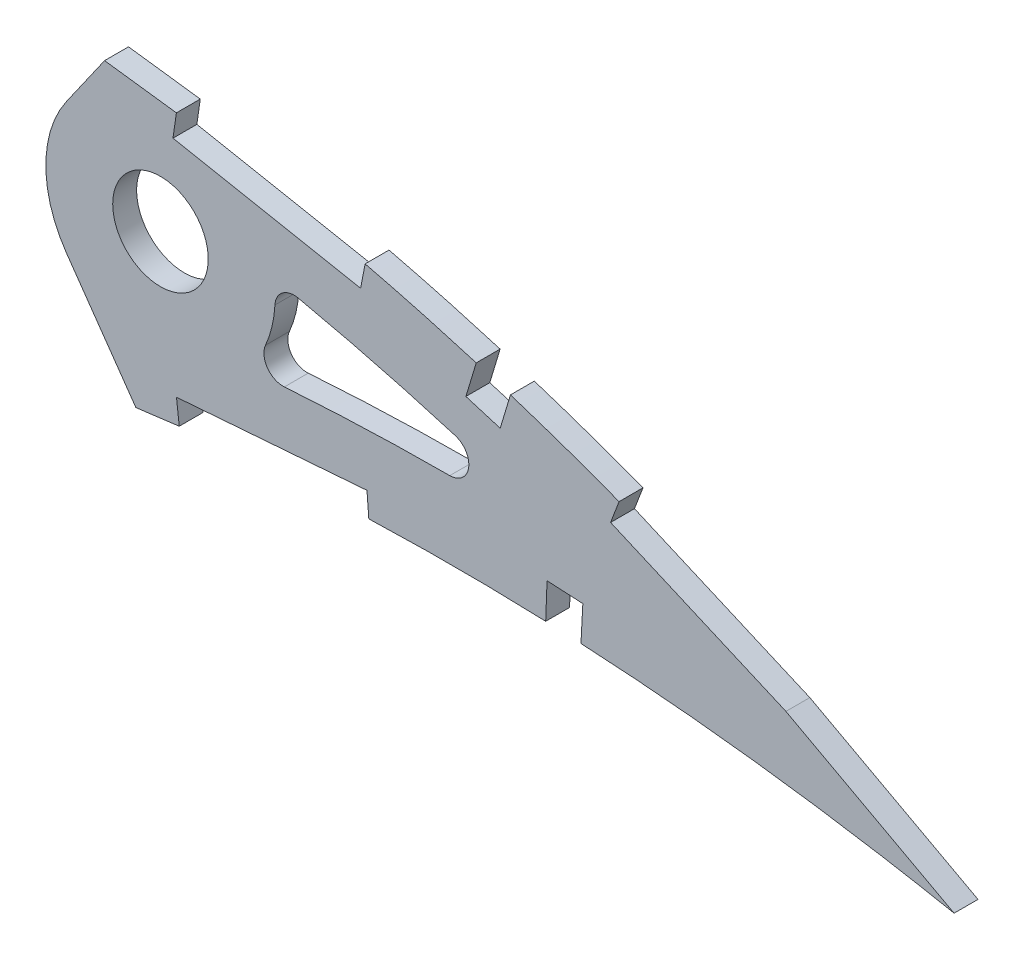
SolidWorks part; units mm, degrees
material "Plywood"
ref_plane "Front Plane" through (0, 0, 0) normal (0, 0, 1) x (1, 0, 0)
ref_plane "Top Plane" through (0, 0, 0) normal (0, 1, 0) x (1, 0, 0)
ref_plane "Right Plane" through (0, 0, 0) normal (1, 0, 0) x (0, 0, -1)
curve "Curve1"
  spline degree 3 poles (383.949, 0.5986, 0) (383.9196, 0.6168, 0) (383.802, 0.6894, 0) (383.5372, 0.8518, 0) (383.0962, 1.1224, 0) (382.4788, 1.4992, 0) (381.6856, 1.9812, 0) (380.716, 2.5651, 0) (379.5708, 3.249, 0) (378.2502, 4.0295, 0) (376.7543, 4.9032, 0) (375.0838, 5.8664, 0) (373.2387, 6.9137, 0) (371.2197, 8.0407, 0) (369.0276, 9.2423, 0) (366.6628, 10.5128, 0) (364.1261, 11.8459, 0) (361.4185, 13.2358, 0) (358.5405, 14.6749, 0) (355.4934, 16.1571, 0) (352.2782, 17.675, 0) (348.8962, 19.2207, 0) (345.3491, 20.7877, 0) (341.638, 22.3663, 0) (337.765, 23.9497, 0) (333.7318, 25.5289, 0) (329.5407, 27.0966, 0) (325.1933, 28.6428, 0) (320.6929, 30.1607, 0) (316.0417, 31.6403, 0) (311.2431, 33.0737, 0) (306.2997, 34.4516, 0) (301.2157, 35.767, 0) (295.9944, 37.0101, 0) (290.6401, 38.1728, 0) (285.1572, 39.2479, 0) (279.5502, 40.2249, 0) (273.8346, 41.1028, 0) (268.1025, 41.8331, 0) (262.3821, 42.5494, 0) (256.6703, 43.2222, 0) (250.8886, 43.8666, 0) (245.0428, 44.4788, 0) (239.1384, 45.057, 0) (233.1816, 45.5987, 0) (227.1785, 46.1022, 0) (221.135, 46.5647, 0) (215.0573, 46.9856, 0) (208.9515, 47.361, 0) (202.8242, 47.6908, 0) (196.6815, 47.9725, 0) (190.5298, 48.2044, 0) (184.3757, 48.385, 0) (178.2255, 48.5125, 0) (172.0859, 48.5861, 0) (165.9633, 48.6039, 0) (159.8643, 48.5655, 0) (153.7954, 48.4696, 0) (147.7632, 48.3149, 0) (141.7741, 48.1011, 0) (135.8345, 47.8283, 0) (129.951, 47.4942, 0) (124.1299, 47.1009, 0) (118.3778, 46.6469, 0) (112.701, 46.1319, 0) (107.1053, 45.5581, 0) (101.5971, 44.9239, 0) (96.1822, 44.2312, 0) (90.8666, 43.4813, 0) (85.6562, 42.6738, 0) (80.5566, 41.8111, 0) (75.5733, 40.894, 0) (70.7116, 39.9252, 0) (65.9768, 38.9049, 0) (61.3739, 37.8363, 0) (56.9076, 36.7211, 0) (52.5828, 35.5615, 0) (48.4038, 34.3602, 0) (44.375, 33.1199, 0) (40.5009, 31.842, 0) (36.7845, 30.5314, 0) (33.2304, 29.1889, 0) (29.8413, 27.8188, 0) (26.6212, 26.4228, 0) (23.5724, 25.0052, 0) (20.6984, 23.5677, 0) (18.0014, 22.1143, 0) (15.4839, 20.6472, 0) (13.1483, 19.1691, 0) (10.9958, 17.6837, 0) (9.0293, 16.1921, 0) (7.2493, 14.698, 0) (5.6571, 13.2036, 0) (4.255, 11.71, 0) (3.0428, 10.2198, 0) (2.0222, 8.7343, 0) (1.1933, 7.2547, 0) (0.558, 5.7822, 0) (0.1157, 4.3176, 0) (-0.1263, 2.863, 0) (-0.1866, 1.4174, 0) (-0.0621, 0.4718, 0) (0, 0, 0) knots 0 0 0 0 0.000254 0.001015 0.002283 0.004057 0.006331 0.009105 0.012374 0.016134 0.02038 0.025106 0.030306 0.035972 0.0421 0.048678 0.055702 0.06316 0.071046 0.07935 0.088063 0.097176 0.106678 0.116562 0.126814 0.137428 0.148394 0.1597 0.171338 0.183298 0.19557 0.208144 0.221012 0.234162 0.247587 0.261277 0.275223 0.289414 0.303771 0.317689 0.331784 0.34604 0.360444 0.374983 0.38964 0.404403 0.419257 0.434187 0.449177 0.464215 0.479284 0.49437 0.509458 0.524532 0.539579 0.554583 0.56953 0.584403 0.599191 0.613877 0.628447 0.642889 0.657186 0.671326 0.685294 0.699078 0.712665 0.726043 0.739198 0.752118 0.764792 0.777208 0.789356 0.801224 0.812804 0.824083 0.835055 0.84571 0.856038 0.866034 0.875689 0.884998 0.893953 0.902553 0.910789 0.918661 0.926166 0.933303 0.940071 0.946475 0.952518 0.958205 0.963547 0.968557 0.97325 0.977651 0.981787 0.985694 0.989415 0.993001 0.996508 1 1 1 1
curve "Curve2"
  spline degree 3 poles (0, 0, 0) (0.0986, -0.4654, 0) (0.2962, -1.3985, 0) (0.8332, -2.7416, 0) (1.5434, -4.0328, 0) (2.4415, -5.2686, 0) (3.5218, -6.4485, 0) (4.7818, -7.574, 0) (6.2202, -8.6443, 0) (7.8352, -9.659, 0) (9.6244, -10.6191, 0) (11.5859, -11.5241, 0) (13.7178, -12.3737, 0) (16.0178, -13.1667, 0) (18.4831, -13.9043, 0) (21.1113, -14.5848, 0) (23.8995, -15.2091, 0) (26.845, -15.7756, 0) (29.9446, -16.2848, 0) (33.195, -16.7366, 0) (36.593, -17.1311, 0) (40.1351, -17.4676, 0) (43.8179, -17.7467, 0) (47.6377, -17.9687, 0) (51.5909, -18.1343, 0) (55.6735, -18.2428, 0) (59.8817, -18.2959, 0) (64.2115, -18.2945, 0) (68.6589, -18.238, 0) (73.2199, -18.1297, 0) (77.8902, -17.9689, 0) (82.6657, -17.7575, 0) (87.5419, -17.4976, 0) (92.5144, -17.1902, 0) (97.5791, -16.8365, 0) (102.7313, -16.4394, 0) (107.9665, -16, 0) (113.2801, -15.5207, 0) (118.6674, -15.0039, 0) (124.1237, -14.4514, 0) (129.6442, -13.8657, 0) (135.2241, -13.2487, 0) (140.8584, -12.6036, 0) (146.5422, -11.9317, 0) (152.2705, -11.2369, 0) (158.0381, -10.5203, 0) (163.84, -9.7848, 0) (169.6711, -9.0339, 0) (175.5259, -8.2674, 0) (181.3995, -7.4908, 0) (187.2862, -6.7036, 0) (193.1809, -5.9096, 0) (199.0781, -5.1115, 0) (204.9721, -4.3094, 0) (210.8578, -3.5066, 0) (216.7295, -2.7054, 0) (222.5817, -1.9059, 0) (228.409, -1.112, 0) (234.2055, -0.3236, 0) (239.9659, 0.4577, 0) (245.6847, 1.2295, 0) (251.3565, 1.9909, 0) (256.9754, 2.7413, 0) (262.5357, 3.4812, 0) (267.9487, 4.188, 0) (273.2002, 4.8993, 0) (278.3079, 5.4825, 0) (283.3519, 5.9802, 0) (288.3377, 6.3883, 0) (293.259, 6.7125, 0) (298.1104, 6.9553, 0) (302.886, 7.1201, 0) (307.5799, 7.2116, 0) (312.186, 7.2323, 0) (316.6983, 7.1886, 0) (321.1107, 7.0842, 0) (325.4171, 6.9238, 0) (329.6115, 6.7126, 0) (333.688, 6.4566, 0) (337.6405, 6.1594, 0) (341.4634, 5.828, 0) (345.1508, 5.4673, 0) (348.6971, 5.0813, 0) (352.0971, 4.6782, 0) (355.3453, 4.2606, 0) (358.4369, 3.8354, 0) (361.3669, 3.4069, 0) (364.1307, 2.9806, 0) (366.7239, 2.5605, 0) (369.1422, 2.1521, 0) (371.3821, 1.7594, 0) (373.4394, 1.3862, 0) (375.3115, 1.0371, 0) (376.9946, 0.7139, 0) (378.4864, 0.4219, 0) (379.7842, 0.1625, 0) (380.886, -0.0608, 0) (381.79, -0.247, 0) (382.4947, -0.3932, 0) (382.9989, -0.4995, 0) (383.3019, -0.5627, 0) (383.4365, -0.5914, 0) (383.4701, -0.5986, 0) knots 0 0 0 0 0.003638 0.007293 0.011028 0.014901 0.018963 0.023258 0.027821 0.032679 0.037853 0.043362 0.049215 0.055422 0.061989 0.068918 0.076211 0.083868 0.091887 0.100266 0.109 0.118085 0.127515 0.137285 0.147388 0.157816 0.168563 0.179619 0.190977 0.202627 0.21456 0.226767 0.239236 0.251959 0.264924 0.27812 0.291536 0.30516 0.318981 0.332985 0.347163 0.361499 0.375981 0.390597 0.405333 0.420175 0.43511 0.450124 0.465203 0.480333 0.495501 0.51069 0.525887 0.541078 0.556247 0.571382 0.586466 0.601485 0.616424 0.631269 0.646007 0.660621 0.675098 0.689423 0.703582 0.716908 0.730009 0.742952 0.755726 0.76832 0.780724 0.792927 0.804916 0.816679 0.828204 0.839475 0.850481 0.861208 0.871639 0.881763 0.891564 0.901027 0.910139 0.918884 0.927249 0.935221 0.942785 0.949928 0.956638 0.962904 0.968712 0.974054 0.978918 0.983297 0.98718 0.990561 0.993433 0.995791 0.99763 0.998946 0.999737 1 1 1 1
sketch "Sketch1" plane through (0, 0, 0) normal (0, 0, 1) x (1, 0, 0)
  line L23 (383.4597, -0.5986) -> (387.1511, -1.386)
  line L24 (383.9386, 0.5986) -> (387.1511, -1.386)
  spline S4 degree 3 poles (0, 0) (0.0986, -0.4654) (0.2962, -1.3984) (0.8332, -2.7416) (1.5433, -4.0327) (2.4415, -5.2684) (3.5217, -6.4484) (4.7816, -7.5738) (6.22, -8.6441) (7.835, -9.6587) (9.6242, -10.6188) (11.5856, -11.5238) (13.7174, -12.3733) (16.0173, -13.1663) (18.4826, -13.9039) (21.1108, -14.5844) (23.8989, -15.2087) (26.8443, -15.7751) (29.9438, -16.2844) (33.1941, -16.7361) (36.592, -17.1306) (40.134, -17.4671) (43.8167, -17.7462) (47.6365, -17.9682) (51.5895, -18.1338) (55.672, -18.2423) (59.88, -18.2954) (64.2098, -18.294) (68.657, -18.2375) (73.2179, -18.1293) (77.8881, -17.9684) (82.6634, -17.757) (87.5395, -17.4972) (92.5119, -17.1897) (97.5764, -16.836) (102.7286, -16.439) (107.9636, -15.9995) (113.2771, -15.5202) (118.6642, -15.0035) (124.1204, -14.451) (129.6407, -13.8653) (135.2204, -13.2483) (140.8546, -12.6033) (146.5382, -11.9314) (152.2664, -11.2365) (158.0338, -10.52) (163.8356, -9.7845) (169.6665, -9.0336) (175.5212, -8.2672) (181.3946, -7.4906) (187.2811, -6.7034) (193.1757, -5.9095) (199.0727, -5.1113) (204.9666, -4.3092) (210.8521, -3.5065) (216.7237, -2.7054) (222.5757, -1.9059) (228.4028, -1.112) (234.1992, -0.3236) (239.9594, 0.4576) (245.6781, 1.2294) (251.3497, 1.9908) (256.9684, 2.7413) (262.5286, 3.4811) (267.9415, 4.1879) (273.1928, 4.8992) (278.3003, 5.4823) (283.3443, 5.98) (288.3299, 6.3881) (293.2511, 6.7123) (298.1023, 6.9552) (302.8778, 7.1199) (307.5715, 7.2114) (312.1776, 7.2321) (316.6897, 7.1884) (321.102, 7.084) (325.4083, 6.9236) (329.6026, 6.7124) (333.679, 6.4564) (337.6313, 6.1592) (341.4541, 5.8278) (345.1414, 5.4671) (348.6876, 5.0812) (352.0875, 4.6781) (355.3357, 4.2605) (358.4272, 3.8353) (361.3571, 3.4068) (364.1208, 2.9805) (366.7139, 2.5604) (369.1322, 2.1521) (371.372, 1.7594) (373.4293, 1.3862) (375.3013, 1.0371) (376.9844, 0.7139) (378.4761, 0.4219) (379.7739, 0.1625) (380.8757, -0.0608) (381.7796, -0.247) (382.4844, -0.3932) (382.9885, -0.4994) (383.2915, -0.5627) (383.4261, -0.5914) (383.4597, -0.5986) knots 0 0 0 0 0.003638 0.007293 0.011028 0.014901 0.018963 0.023258 0.027821 0.032679 0.037853 0.043362 0.049215 0.055422 0.061989 0.068918 0.076211 0.083868 0.091887 0.100266 0.109 0.118085 0.127515 0.137285 0.147388 0.157816 0.168563 0.179619 0.190977 0.202627 0.21456 0.226767 0.239236 0.251959 0.264924 0.27812 0.291536 0.30516 0.318981 0.332985 0.347163 0.361499 0.375981 0.390597 0.405333 0.420175 0.43511 0.450124 0.465203 0.480333 0.495501 0.51069 0.525887 0.541078 0.556247 0.571382 0.586466 0.601485 0.616424 0.631269 0.646007 0.660621 0.675098 0.689423 0.703582 0.716908 0.730009 0.742952 0.755726 0.76832 0.780724 0.792927 0.804916 0.816679 0.828204 0.839475 0.850481 0.861208 0.871639 0.881763 0.891564 0.901027 0.910139 0.918884 0.927249 0.935221 0.942785 0.949928 0.956638 0.962904 0.968712 0.974054 0.978918 0.983297 0.98718 0.990561 0.993433 0.995791 0.99763 0.998946 0.999737 1 1 1 1
  spline S5 degree 3 poles (383.9386, 0.5986) (383.9092, 0.6167) (383.7916, 0.6893) (383.5268, 0.8518) (383.0858, 1.1223) (382.4685, 1.4991) (381.6752, 1.9811) (380.7057, 2.565) (379.5606, 3.2489) (378.24, 4.0294) (376.7441, 4.9031) (375.0736, 5.8662) (373.2286, 6.9135) (371.2097, 8.0405) (369.0176, 9.242) (366.6529, 10.5125) (364.1162, 11.8456) (361.4087, 13.2354) (358.5307, 14.6745) (355.4837, 16.1566) (352.2687, 17.6745) (348.8867, 19.2201) (345.3398, 20.7871) (341.6288, 22.3657) (337.7559, 23.949) (333.7228, 25.5282) (329.5317, 27.0959) (325.1845, 28.642) (320.6843, 30.1598) (316.0332, 31.6395) (311.2346, 33.0728) (306.2914, 34.4507) (301.2076, 35.766) (295.9864, 37.0091) (290.6322, 38.1717) (285.1495, 39.2469) (279.5426, 40.2238) (273.8272, 41.1017) (268.0952, 41.832) (262.375, 42.5482) (256.6633, 43.2211) (250.8818, 43.8654) (245.0361, 44.4776) (239.1319, 45.0558) (233.1753, 45.5974) (227.1724, 46.1009) (221.129, 46.5635) (215.0515, 46.9843) (208.9459, 47.3597) (202.8187, 47.6895) (196.6762, 47.9712) (190.5246, 48.2031) (184.3707, 48.3836) (178.2206, 48.5111) (172.0812, 48.5848) (165.9588, 48.6026) (159.86, 48.5642) (153.7912, 48.4683) (147.7592, 48.3136) (141.7702, 48.0998) (135.8308, 47.827) (129.9475, 47.4929) (124.1266, 47.0997) (118.3746, 46.6456) (112.6979, 46.1306) (107.1024, 45.5568) (101.5944, 44.9227) (96.1796, 44.23) (90.8641, 43.4801) (85.6539, 42.6727) (80.5544, 41.81) (75.5713, 40.8929) (70.7097, 39.9241) (65.975, 38.9039) (61.3722, 37.8353) (56.906, 36.7201) (52.5814, 35.5606) (48.4025, 34.3593) (44.3738, 33.119) (40.4998, 31.8412) (36.7835, 30.5306) (33.2295, 29.1881) (29.8405, 27.818) (26.6204, 26.4221) (23.5718, 25.0045) (20.6979, 23.5671) (18.0009, 22.1137) (15.4834, 20.6466) (13.148, 19.1685) (10.9955, 17.6833) (9.029, 16.1917) (7.2491, 14.6976) (5.657, 13.2033) (4.2548, 11.7097) (3.0427, 10.2196) (2.0221, 8.734) (1.1932, 7.2545) (0.558, 5.782) (0.1157, 4.3174) (-0.1263, 2.8629) (-0.1866, 1.4173) (-0.0621, 0.4717) (0, 0) knots 0 0 0 0 0.000254 0.001015 0.002283 0.004057 0.006331 0.009105 0.012374 0.016134 0.02038 0.025106 0.030306 0.035972 0.0421 0.048678 0.055702 0.06316 0.071046 0.07935 0.088063 0.097176 0.106678 0.116562 0.126814 0.137428 0.148394 0.1597 0.171338 0.183298 0.19557 0.208144 0.221012 0.234162 0.247587 0.261277 0.275223 0.289414 0.303771 0.317689 0.331784 0.34604 0.360444 0.374983 0.38964 0.404403 0.419257 0.434187 0.449177 0.464215 0.479284 0.49437 0.509458 0.524532 0.539579 0.554583 0.56953 0.584403 0.599191 0.613877 0.628447 0.642889 0.657186 0.671326 0.685294 0.699078 0.712665 0.726043 0.739198 0.752118 0.764792 0.777208 0.789356 0.801224 0.812804 0.824083 0.835055 0.84571 0.856038 0.866034 0.875689 0.884998 0.893953 0.902553 0.910789 0.918661 0.926166 0.933303 0.940071 0.946475 0.952518 0.958205 0.963547 0.968557 0.97325 0.977651 0.981787 0.985694 0.989415 0.993001 0.996508 1 1 1 1
extrude "Boss-Extrude1" add sketch "Sketch1" along normal blind 3.175
sketch "Sketch3" plane through (0, 0, 0) normal (0, 0, -1) x (-1, 0, 0)
  circle A1 centre (-272.4199, 26.2554) radius 6.35
extrude "Cut-Extrude2" cut sketch "Sketch3" against normal blind 7.62
sketch "Sketch4" plane through (0, 0, 3.175) normal (0, 0, 1) x (1, 0, 0)
  line L0 (272.4199, 26.2554) -> (275.6183, 26.2554)
  line L1 (259.936, 34.9967) -> (264.9932, 42.2191)
  line L2 (259.936, 17.5141) -> (269.1511, 4.3535)
  circle A0 centre (272.4199, 26.2554) radius 6.35 construction
  circle A1 centre (272.4199, 26.2554) radius 6.35
  circle A2 centre (272.4199, 26.2554) radius 15.24
  spline S0 degree 3 poles (-2900.5811, -762.1564) (60.7171, 58.1372) (-7.1311, 17.1797) (0.8332, -2.7416) (1.5433, -4.0327) (2.4415, -5.2684) (3.5217, -6.4484) (4.7816, -7.5738) (6.22, -8.6441) (7.835, -9.6587) (9.6242, -10.6188) (11.5856, -11.5238) (13.7174, -12.3733) (16.0173, -13.1663) (18.4826, -13.9039) (21.1108, -14.5844) (23.8989, -15.2087) (26.8443, -15.7751) (29.9438, -16.2844) (33.1941, -16.7361) (36.592, -17.1306) (40.134, -17.4671) (43.8167, -17.7462) (47.6365, -17.9682) (51.5895, -18.1338) (55.672, -18.2423) (59.88, -18.2954) (64.2098, -18.294) (68.657, -18.2375) (73.2179, -18.1293) (77.8881, -17.9684) (82.6634, -17.757) (87.5395, -17.4972) (92.5119, -17.1897) (97.5764, -16.836) (102.7286, -16.439) (107.9636, -15.9995) (113.2771, -15.5202) (118.6642, -15.0035) (124.1204, -14.451) (129.6407, -13.8653) (135.2204, -13.2483) (140.8546, -12.6033) (146.5382, -11.9314) (152.2664, -11.2365) (158.0338, -10.52) (163.8356, -9.7845) (169.6665, -9.0336) (175.5212, -8.2672) (181.3946, -7.4906) (187.2811, -6.7034) (193.1757, -5.9095) (199.0727, -5.1113) (204.9666, -4.3092) (210.8521, -3.5065) (216.7237, -2.7054) (222.5757, -1.9059) (228.4028, -1.112) (234.1992, -0.3236) (239.9594, 0.4576) (245.6781, 1.2294) (251.3497, 1.9908) (256.9684, 2.7413) (262.5286, 3.4811) (267.9415, 4.1879) (273.1928, 4.8992) (278.3003, 5.4823) (283.3443, 5.98) (288.3299, 6.3881) (293.2511, 6.7123) (298.1023, 6.9552) (302.8778, 7.1199) (307.5715, 7.2114) (312.1776, 7.2321) (316.6897, 7.1884) (321.102, 7.084) (325.4083, 6.9236) (329.6026, 6.7124) (333.679, 6.4564) (337.6313, 6.1592) (341.4541, 5.8278) (345.1414, 5.4671) (348.6876, 5.0812) (352.0875, 4.6781) (355.3357, 4.2605) (358.4272, 3.8353) (361.3571, 3.4068) (364.1208, 2.9805) (366.7139, 2.5604) (369.1322, 2.1521) (371.372, 1.7594) (373.4293, 1.3862) (375.3013, 1.0371) (376.9844, 0.7139) (378.4761, 0.4219) (379.7739, 0.1625) (380.8757, -0.0608) (381.7796, -0.247) (382.4844, -0.3932) (382.9885, -0.4994) (397.7614, -3.5828) (410.8952, -13.5854) (1047.3532, 2924.2375) knots -0.152541 -0.152541 -0.152541 -0.152541 0.003638 0.007293 0.011028 0.014901 0.018963 0.023258 0.027821 0.032679 0.037853 0.043362 0.049215 0.055422 0.061989 0.068918 0.076211 0.083868 0.091887 0.100266 0.109 0.118085 0.127515 0.137285 0.147388 0.157816 0.168563 0.179619 0.190977 0.202627 0.21456 0.226767 0.239236 0.251959 0.264924 0.27812 0.291536 0.30516 0.318981 0.332985 0.347163 0.361499 0.375981 0.390597 0.405333 0.420175 0.43511 0.450124 0.465203 0.480333 0.495501 0.51069 0.525887 0.541078 0.556247 0.571382 0.586466 0.601485 0.616424 0.631269 0.646007 0.660621 0.675098 0.689423 0.703582 0.716908 0.730009 0.742952 0.755726 0.76832 0.780724 0.792927 0.804916 0.816679 0.828204 0.839475 0.850481 0.861208 0.871639 0.881763 0.891564 0.901027 0.910139 0.918884 0.927249 0.935221 0.942785 0.949928 0.956638 0.962904 0.968712 0.974054 0.978918 0.983297 0.98718 0.990561 0.993433 0.995791 0.99763 0.998946 0.999737 1.113214 1.113214 1.113214 1.113214 only from (0, 0) to (383.4597, -0.5986) construction
  spline S1 degree 3 poles (1998.8466, 2527.3991) (408.7537, -22.1004) (397.8856, -7.9557) (383.5268, 0.8518) (383.0858, 1.1223) (382.4685, 1.4991) (381.6752, 1.9811) (380.7057, 2.565) (379.5606, 3.2489) (378.24, 4.0294) (376.7441, 4.9031) (375.0736, 5.8662) (373.2286, 6.9135) (371.2097, 8.0405) (369.0176, 9.242) (366.6529, 10.5125) (364.1162, 11.8456) (361.4087, 13.2354) (358.5307, 14.6745) (355.4837, 16.1566) (352.2687, 17.6745) (348.8867, 19.2201) (345.3398, 20.7871) (341.6288, 22.3657) (337.7559, 23.949) (333.7228, 25.5282) (329.5317, 27.0959) (325.1845, 28.642) (320.6843, 30.1598) (316.0332, 31.6395) (311.2346, 33.0728) (306.2914, 34.4507) (301.2076, 35.766) (295.9864, 37.0091) (290.6322, 38.1717) (285.1495, 39.2469) (279.5426, 40.2238) (273.8272, 41.1017) (268.0952, 41.832) (262.375, 42.5482) (256.6633, 43.2211) (250.8818, 43.8654) (245.0361, 44.4776) (239.1319, 45.0558) (233.1753, 45.5974) (227.1724, 46.1009) (221.129, 46.5635) (215.0515, 46.9843) (208.9459, 47.3597) (202.8187, 47.6895) (196.6762, 47.9712) (190.5246, 48.2031) (184.3707, 48.3836) (178.2206, 48.5111) (172.0812, 48.5848) (165.9588, 48.6026) (159.86, 48.5642) (153.7912, 48.4683) (147.7592, 48.3136) (141.7702, 48.0998) (135.8308, 47.827) (129.9475, 47.4929) (124.1266, 47.0997) (118.3746, 46.6456) (112.6979, 46.1306) (107.1024, 45.5568) (101.5944, 44.9227) (96.1796, 44.23) (90.8641, 43.4801) (85.6539, 42.6727) (80.5544, 41.81) (75.5713, 40.8929) (70.7097, 39.9241) (65.975, 38.9039) (61.3722, 37.8353) (56.906, 36.7201) (52.5814, 35.5606) (48.4025, 34.3593) (44.3738, 33.119) (40.4998, 31.8412) (36.7835, 30.5306) (33.2295, 29.1881) (29.8405, 27.818) (26.6204, 26.4221) (23.5718, 25.0045) (20.6979, 23.5671) (18.0009, 22.1137) (15.4834, 20.6466) (13.148, 19.1685) (10.9955, 17.6833) (9.029, 16.1917) (7.2491, 14.6976) (5.657, 13.2033) (4.2548, 11.7097) (3.0427, 10.2196) (2.0221, 8.734) (1.1932, 7.2545) (0.558, 5.782) (0.1157, 4.3174) (-0.1263, 2.8629) (-1.0184, -18.5368) (76.7539, -34.5403) (-2989.0976, -246.1964) knots -0.121519 -0.121519 -0.121519 -0.121519 0.000254 0.001015 0.002283 0.004057 0.006331 0.009105 0.012374 0.016134 0.02038 0.025106 0.030306 0.035972 0.0421 0.048678 0.055702 0.06316 0.071046 0.07935 0.088063 0.097176 0.106678 0.116562 0.126814 0.137428 0.148394 0.1597 0.171338 0.183298 0.19557 0.208144 0.221012 0.234162 0.247587 0.261277 0.275223 0.289414 0.303771 0.317689 0.331784 0.34604 0.360444 0.374983 0.38964 0.404403 0.419257 0.434187 0.449177 0.464215 0.479284 0.49437 0.509458 0.524532 0.539579 0.554583 0.56953 0.584403 0.599191 0.613877 0.628447 0.642889 0.657186 0.671326 0.685294 0.699078 0.712665 0.726043 0.739198 0.752118 0.764792 0.777208 0.789356 0.801224 0.812804 0.824083 0.835055 0.84571 0.856038 0.866034 0.875689 0.884998 0.893953 0.902553 0.910789 0.918661 0.926166 0.933303 0.940071 0.946475 0.952518 0.958205 0.963547 0.968557 0.97325 0.977651 0.981787 0.985694 0.989415 0.993001 0.996508 1.146107 1.146107 1.146107 1.146107 only from (383.9386, 0.5986) to (0, 0) construction
  spline S2 degree 3 poles (161.4571, -10.0855) (162.2464, -9.9853) (164.9804, -9.6371) (169.6665, -9.0336) (175.5212, -8.2672) (181.3946, -7.4906) (187.2811, -6.7034) (193.1757, -5.9095) (199.0727, -5.1113) (204.9666, -4.3092) (210.8521, -3.5065) (216.7237, -2.7054) (222.5757, -1.9059) (228.4028, -1.112) (234.1992, -0.3236) (239.9594, 0.4576) (245.6781, 1.2294) (251.3497, 1.9908) (256.9684, 2.7413) (262.5286, 3.4811) (267.9415, 4.1879) (273.1928, 4.8992) (278.3003, 5.4823) (283.3443, 5.98) (288.3299, 6.3881) (293.2511, 6.7123) (298.1023, 6.9552) (302.8778, 7.1199) (307.5715, 7.2114) (312.1776, 7.2321) (316.6897, 7.1884) (321.102, 7.084) (325.4083, 6.9236) (329.6026, 6.7124) (333.679, 6.4564) (337.6313, 6.1592) (341.4541, 5.8278) (345.1414, 5.4671) (348.6876, 5.0812) (352.0875, 4.6781) (355.3357, 4.2605) (358.4272, 3.8353) (361.3571, 3.4068) (364.1208, 2.9805) (366.7139, 2.5604) (369.1322, 2.1521) (371.372, 1.7594) (373.4293, 1.3862) (375.3013, 1.0371) (376.9844, 0.7139) (378.4761, 0.4219) (379.7739, 0.1625) (380.8757, -0.0608) (381.7796, -0.247) (382.4844, -0.3932) (382.9885, -0.4994) (383.2915, -0.5627) (383.4261, -0.5914) (383.4597, -0.5986) knots 0.429016 0.429016 0.429016 0.429016 0.43511 0.450124 0.465203 0.480333 0.495501 0.51069 0.525887 0.541078 0.556247 0.571382 0.586466 0.601485 0.616424 0.631269 0.646007 0.660621 0.675098 0.689423 0.703582 0.716908 0.730009 0.742952 0.755726 0.76832 0.780724 0.792927 0.804916 0.816679 0.828204 0.839475 0.850481 0.861208 0.871639 0.881763 0.891564 0.901027 0.910139 0.918884 0.927249 0.935221 0.942785 0.949928 0.956638 0.962904 0.968712 0.974054 0.978918 0.983297 0.98718 0.990561 0.993433 0.995791 0.99763 0.998946 0.999737 1 1 1 1
  spline S3 degree 3 poles (383.9386, 0.5986) (383.9092, 0.6167) (383.7916, 0.6893) (383.5268, 0.8518) (383.0858, 1.1223) (382.4685, 1.4991) (381.6752, 1.9811) (380.7057, 2.565) (379.5606, 3.2489) (378.24, 4.0294) (376.7441, 4.9031) (375.0736, 5.8662) (373.2286, 6.9135) (371.2097, 8.0405) (369.0176, 9.242) (366.6529, 10.5125) (364.1162, 11.8456) (361.4087, 13.2354) (358.5307, 14.6745) (355.4837, 16.1566) (352.2687, 17.6745) (348.8867, 19.2201) (345.3398, 20.7871) (341.6288, 22.3657) (337.7559, 23.949) (333.7228, 25.5282) (329.5317, 27.0959) (325.1845, 28.642) (320.6843, 30.1598) (316.0332, 31.6395) (311.2346, 33.0728) (306.2914, 34.4507) (301.2076, 35.766) (295.9864, 37.0091) (290.6322, 38.1717) (285.1495, 39.2469) (279.5426, 40.2238) (273.8272, 41.1017) (268.0952, 41.832) (262.375, 42.5482) (256.6633, 43.2211) (250.8818, 43.8654) (245.0361, 44.4776) (239.1319, 45.0558) (233.1753, 45.5974) (227.1724, 46.1009) (221.129, 46.5635) (215.0515, 46.9843) (208.9459, 47.3597) (202.8187, 47.6895) (196.6762, 47.9712) (190.5246, 48.2031) (184.3707, 48.3836) (178.2206, 48.5111) (172.0812, 48.5848) (165.9588, 48.6026) (159.86, 48.5642) (153.5038, 48.4638) (149.182, 48.3499) (146.8838, 48.276) knots 0 0 0 0 0.000254 0.001015 0.002283 0.004057 0.006331 0.009105 0.012374 0.016134 0.02038 0.025106 0.030306 0.035972 0.0421 0.048678 0.055702 0.06316 0.071046 0.07935 0.088063 0.097176 0.106678 0.116562 0.126814 0.137428 0.148394 0.1597 0.171338 0.183298 0.19557 0.208144 0.221012 0.234162 0.247587 0.261277 0.275223 0.289414 0.303771 0.317689 0.331784 0.34604 0.360444 0.374983 0.38964 0.404403 0.419257 0.434187 0.449177 0.464215 0.479284 0.49437 0.509458 0.524532 0.539579 0.554583 0.56953 0.584403 0.601304 0.601304 0.601304 0.601304
  spline S4 degree 1 poles (378.5989, -8.0451) (147.21, 38.1213) knots 0 0 1 1 construction
  spline S5 degree 3 poles (378.5989, -8.0451) (378.472, -7.9667) (378.2234, -7.8142) (377.6805, -7.4812) (376.7611, -6.9205) (374.9109, -5.8032) (371.1788, -3.5966) (363.6516, 0.6712) (348.2892, 8.639) (330.0962, 16.359) (311.3792, 22.5636) (297.107, 26.4342) (285.0856, 28.9814) (276.5539, 30.4164) (271.7323, 31.12) (268.0333, 31.5987) (264.2273, 32.0776) (259.2208, 32.6948) (250.4292, 33.7129) (237.8617, 35.009) (222.7587, 36.2937) (202.6061, 37.6338) (177.3909, 38.5745) (157.2697, 38.4445) (147.21, 38.1213) knots 0 0 0 0 0.001174 0.002349 0.004698 0.009395 0.018791 0.037581 0.075163 0.150326 0.187907 0.225489 0.26307 0.281861 0.291256 0.300652 0.310047 0.319443 0.338233 0.375815 0.413396 0.450978 0.526141 0.601304 0.601304 0.601304 0.601304
  spline S6 degree 1 poles (160.178, -0.0063) (385.5793, 9.3379) knots 0 0 1 1 construction
  spline S7 degree 3 poles (160.178, -0.0063) (169.3975, 1.1637) (187.8091, 3.6001) (210.885, 6.7523) (229.3545, 9.2731) (243.2292, 11.1537) (254.7583, 12.7013) (262.905, 13.7751) (267.4672, 14.3775) (270.981, 14.8497) (274.6098, 15.2908) (279.3773, 15.8089) (285.3756, 16.3645) (292.5728, 16.8641) (302.1885, 17.3159) (314.2133, 17.4755) (333.4344, 16.8874) (352.5648, 15.0706) (369.1185, 12.5101) (377.3698, 10.9967) (381.4564, 10.1902) (383.3728, 9.7984) (384.2388, 9.6192) (384.6955, 9.524) (385.0455, 9.4502) (385.329, 9.391) (385.4982, 9.3552) (385.5793, 9.3379) knots 0.429016 0.429016 0.429016 0.429016 0.500389 0.571762 0.607448 0.643135 0.678821 0.696665 0.705586 0.714508 0.723429 0.732351 0.750194 0.768038 0.785881 0.821567 0.857254 0.928627 0.964313 0.982157 0.991078 0.995539 0.996654 0.99777 0.998885 0.999442 1 1 1 1
  dimension "D1" = 30.48
  dimension "D2" = 55
  dimension "D3" = 55
  dimension "D4" = 10.16
extrude "Cut-Extrude3" cut sketch "Sketch4" against normal through all
sketch "Sketch5" plane through (0, 0, 3.175) normal (0, 0, 1) x (1, 0, 0)
  line L0 (274.5345, 40.976) -> (274.083, 37.8333)
  line L1 (274.083, 37.8333) -> (299.0226, 33.019)
  line L2 (299.0226, 33.019) -> (299.6244, 36.1364)
  line L3 (274.9174, 5.0903) -> (274.5453, 8.2434)
  line L4 (274.5453, 8.2434) -> (299.8708, 10.1869)
  line L5 (299.8708, 10.1869) -> (300.1138, 7.0212)
  line L6 (333.3826, 25.6462) -> (332.2514, 22.6795)
  line L7 (332.2514, 22.6795) -> (355.5602, 12.5869)
  line L8 (355.5602, 12.5869) -> (377.9168, 0.5311)
  line L9 (377.9168, 0.5311) -> (379.5381, 3.2609)
  line L10 (355.5602, 12.5869) -> (356.9478, 15.4426)
  line L11 (314.393, 32.1244) -> (313.0177, 27.5648)
  line L12 (313.0177, 27.5648) -> (317.5773, 26.1895)
  line L13 (317.5773, 26.1895) -> (318.9408, 30.7101)
  line L14 (323.625, 6.9875) -> (323.8072, 11.7465)
  line L15 (323.8072, 11.7465) -> (328.5631, 11.4961)
  line L16 (328.5631, 11.4961) -> (328.3145, 6.7742)
  line L17 (333.3826, 25.6462) -> (318.9408, 30.7101) construction
  line L18 (314.393, 32.1244) -> (299.6244, 36.1364) construction
  line L19 (355.5602, 12.5869) -> (351.7355, 4.7158)
  line L20 (351.7355, 4.7158) -> (328.3145, 6.7742) construction
  line L21 (323.625, 6.9875) -> (300.1138, 7.0212) construction
  circle A0 centre (272.4199, 26.2554) radius 6.35 construction
  circle A1 centre (272.4199, 26.2554) radius 6.35
  spline S0 degree 3 poles (-210.4395, 1941.1642) (121.3297, -52.1941) (196.4933, -3.8575) (278.3003, 5.4823) (283.3443, 5.98) (288.3299, 6.3881) (293.2511, 6.7123) (298.1023, 6.9552) (302.8778, 7.1199) (307.5715, 7.2114) (312.1776, 7.2321) (316.6897, 7.1884) (321.102, 7.084) (325.4083, 6.9236) (329.6026, 6.7124) (333.679, 6.4564) (337.6313, 6.1592) (341.4541, 5.8278) (345.1414, 5.4671) (348.6876, 5.0812) (352.0875, 4.6781) (355.3357, 4.2605) (358.4272, 3.8353) (361.3571, 3.4068) (364.1208, 2.9805) (366.7139, 2.5604) (369.1322, 2.1521) (371.372, 1.7594) (373.4293, 1.3862) (375.3013, 1.0371) (376.9844, 0.7139) (378.4761, 0.4219) (379.7739, 0.1625) (380.8757, -0.0608) (381.7796, -0.247) (382.4844, -0.3932) (382.9885, -0.4994) (395.9321, -3.201) (407.582, -11.1888) (835.0263, 1947.3652) knots 0.11236 0.11236 0.11236 0.11236 0.716908 0.730009 0.742952 0.755726 0.76832 0.780724 0.792927 0.804916 0.816679 0.828204 0.839475 0.850481 0.861208 0.871639 0.881763 0.891564 0.901027 0.910139 0.918884 0.927249 0.935221 0.942785 0.949928 0.956638 0.962904 0.968712 0.974054 0.978918 0.983297 0.98718 0.990561 0.993433 0.995791 0.99763 0.998946 0.999737 1.098901 1.098901 1.098901 1.098901 only from (269.1511, 4.3535) to (383.4597, -0.5986) construction
  spline S1 degree 3 poles (1469.2762, 1679.7392) (405.976, -18.6391) (396.1038, -6.8628) (383.5268, 0.8518) (383.0858, 1.1223) (382.4685, 1.4991) (381.6752, 1.9811) (380.7057, 2.565) (379.5606, 3.2489) (378.24, 4.0294) (376.7441, 4.9031) (375.0736, 5.8662) (373.2286, 6.9135) (371.2097, 8.0405) (369.0176, 9.242) (366.6529, 10.5125) (364.1162, 11.8456) (361.4087, 13.2354) (358.5307, 14.6745) (355.4837, 16.1566) (352.2687, 17.6745) (348.8867, 19.2201) (345.3398, 20.7871) (341.6288, 22.3657) (337.7559, 23.949) (333.7228, 25.5282) (329.5317, 27.0959) (325.1845, 28.642) (320.6843, 30.1598) (316.0332, 31.6395) (311.2346, 33.0728) (306.2914, 34.4507) (301.2076, 35.766) (295.9864, 37.0091) (290.6322, 38.1717) (285.1495, 39.2469) (279.5426, 40.2238) (273.8272, 41.1017) (132.45, 59.114) (-8.1155, 65.8482) (-401.8712, -1828.0204) knots -0.106157 -0.106157 -0.106157 -0.106157 0.000254 0.001015 0.002283 0.004057 0.006331 0.009105 0.012374 0.016134 0.02038 0.025106 0.030306 0.035972 0.0421 0.048678 0.055702 0.06316 0.071046 0.07935 0.088063 0.097176 0.106678 0.116562 0.126814 0.137428 0.148394 0.1597 0.171338 0.183298 0.19557 0.208144 0.221012 0.234162 0.247587 0.261277 0.275223 0.289414 0.303771 1.322643 1.322643 1.322643 1.322643 only from (383.9386, 0.5986) to (264.9932, 42.2191) construction
  spline S2 degree 3 poles (269.1511, 4.3535) (270.5083, 4.5347) (273.5611, 4.9412) (278.3003, 5.4823) (283.3443, 5.98) (288.3299, 6.3881) (293.2511, 6.7123) (298.1023, 6.9552) (302.8778, 7.1199) (307.5715, 7.2114) (312.1776, 7.2321) (316.6897, 7.1884) (321.102, 7.084) (325.4083, 6.9236) (329.6026, 6.7124) (333.679, 6.4564) (337.6313, 6.1592) (341.4541, 5.8278) (345.1414, 5.4671) (348.6876, 5.0812) (352.0875, 4.6781) (355.3357, 4.2605) (358.4272, 3.8353) (361.3571, 3.4068) (364.1208, 2.9805) (366.7139, 2.5604) (369.1322, 2.1521) (371.372, 1.7594) (373.4293, 1.3862) (375.3013, 1.0371) (376.9844, 0.7139) (378.4761, 0.4219) (379.7739, 0.1625) (380.8757, -0.0608) (381.7796, -0.247) (382.4844, -0.3932) (382.9885, -0.4994) (383.2915, -0.5627) (383.4261, -0.5914) (383.4597, -0.5986) knots 0.706421 0.706421 0.706421 0.706421 0.716908 0.730009 0.742952 0.755726 0.76832 0.780724 0.792927 0.804916 0.816679 0.828204 0.839475 0.850481 0.861208 0.871639 0.881763 0.891564 0.901027 0.910139 0.918884 0.927249 0.935221 0.942785 0.949928 0.956638 0.962904 0.968712 0.974054 0.978918 0.983297 0.98718 0.990561 0.993433 0.995791 0.99763 0.998946 0.999737 1 1 1 1
  spline S3 degree 3 poles (383.9386, 0.5986) (383.9092, 0.6167) (383.7916, 0.6893) (383.5268, 0.8518) (383.0858, 1.1223) (382.4685, 1.4991) (381.6752, 1.9811) (380.7057, 2.565) (379.5606, 3.2489) (378.24, 4.0294) (376.7441, 4.9031) (375.0736, 5.8662) (373.2286, 6.9135) (371.2097, 8.0405) (369.0176, 9.242) (366.6529, 10.5125) (364.1162, 11.8456) (361.4087, 13.2354) (358.5307, 14.6745) (355.4837, 16.1566) (352.2687, 17.6745) (348.8867, 19.2201) (345.3398, 20.7871) (341.6288, 22.3657) (337.7559, 23.949) (333.7228, 25.5282) (329.5317, 27.0959) (325.1845, 28.642) (320.6843, 30.1598) (316.0332, 31.6395) (311.2346, 33.0728) (306.2914, 34.4507) (301.2076, 35.766) (295.9864, 37.0091) (290.6322, 38.1717) (285.1495, 39.2469) (279.5426, 40.2238) (273.8272, 41.1017) (268.9598, 41.7218) (266.0075, 42.093) (264.9932, 42.2191) knots 0 0 0 0 0.000254 0.001015 0.002283 0.004057 0.006331 0.009105 0.012374 0.016134 0.02038 0.025106 0.030306 0.035972 0.0421 0.048678 0.055702 0.06316 0.071046 0.07935 0.088063 0.097176 0.106678 0.116562 0.126814 0.137428 0.148394 0.1597 0.171338 0.183298 0.19557 0.208144 0.221012 0.234162 0.247587 0.261277 0.275223 0.289414 0.303771 0.311283 0.311283 0.311283 0.311283
  dimension "D1" = 3.175
  dimension "D2" = 25.4
  dimension "D3" = 4.7625
extrude "Cut-Extrude4" cut sketch "Sketch5" against normal through all
fillet "Fillet1" radius 2.54 3 edges at (327.5492, 16.986, 1.5875) (287.5051, 28.4217, 1.5875) (283.8824, 16.2121, 1.5875)
move or copy body "Body-Move/Copy1" [suppressed] bodies to move or copy 119 parameters "D1"=0, "D2"=0, "D3"=0
